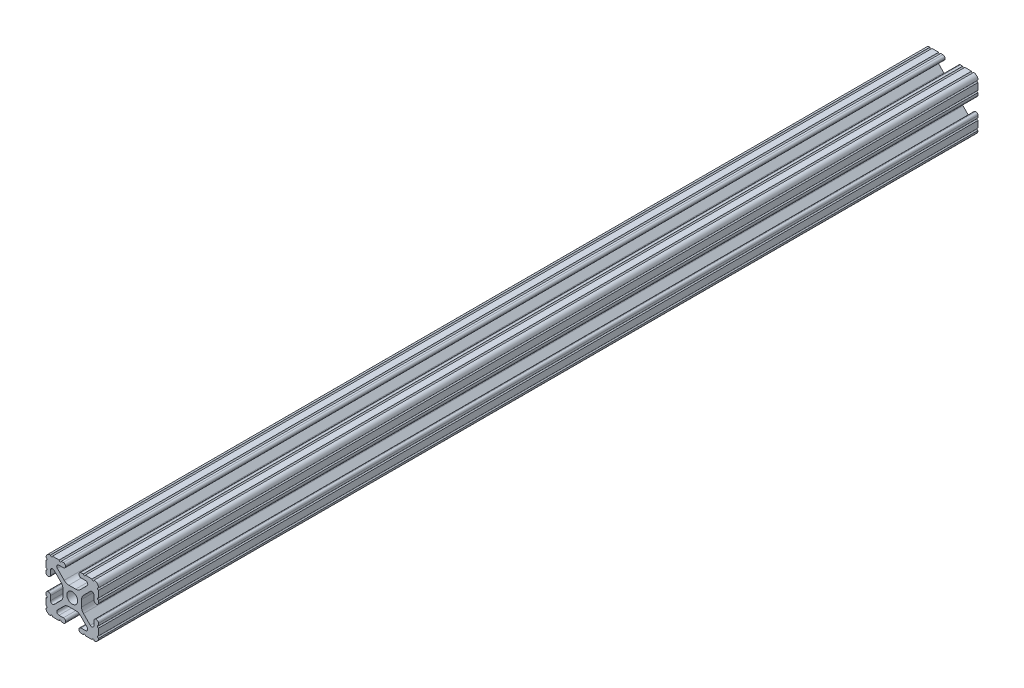
SolidWorks part; units mm, degrees
ref_plane "Front Plane" through (0, 0, 0) normal (0, 0, 1) x (1, 0, 0)
ref_plane "Top Plane" through (0, 0, 0) normal (0, 1, 0) x (1, 0, 0)
ref_plane "Right Plane" through (0, 0, 0) normal (1, 0, 0) x (0, 0, -1)
sketch "Sketch1" plane through (0, 0, 0) normal (0, 0, 1) x (1, 0, 0)
  line L88 (-7.1797, -8.6452) -> (-3.9523, -5.4237)
  line L89 (-1.7093, -4.4958) -> (1.7093, -4.4958)
  line L90 (3.9523, -5.4237) -> (7.1797, -8.6452)
  line L91 (6.4164, -10.4902) -> (4.2875, -10.4902)
  line L92 (3.2385, -11.5392) -> (3.2385, -11.651)
  line L93 (4.2875, -12.7) -> (5.3171, -12.7)
  line L94 (6.3331, -12.7) -> (9.5504, -12.7)
  line L95 (12.7, -9.5504) -> (12.7, -6.3331)
  line L96 (12.7, -5.3171) -> (12.7, -4.2875)
  line L97 (11.651, -3.2385) -> (11.5392, -3.2385)
  line L98 (10.4902, -4.2875) -> (10.4902, -6.4021)
  line L99 (8.7371, -7.1294) -> (5.441, -3.8408)
  line L100 (4.5085, -1.5932) -> (4.5085, 1.5932)
  line L101 (5.441, 3.8408) -> (8.7371, 7.1294)
  line L102 (10.4902, 6.4021) -> (10.4902, 4.2875)
  line L103 (11.5392, 3.2385) -> (11.651, 3.2385)
  line L104 (12.7, 4.2875) -> (12.7, 5.3171)
  line L105 (12.7, 6.3331) -> (12.7, 9.5504)
  line L106 (9.5504, 12.7) -> (6.3331, 12.7)
  line L107 (5.3171, 12.7) -> (4.2875, 12.7)
  line L108 (3.2385, 11.651) -> (3.2385, 11.5392)
  line L109 (4.2875, 10.4902) -> (6.4768, 10.4902)
  line L110 (7.207, 8.7244) -> (3.8983, 5.4232)
  line L111 (1.6558, 4.4958) -> (-1.6558, 4.4958)
  line L112 (-3.8983, 5.4232) -> (-7.207, 8.7244)
  line L113 (-6.4768, 10.4902) -> (-4.2875, 10.4902)
  line L114 (-3.2385, 11.5392) -> (-3.2385, 11.651)
  line L115 (-4.2875, 12.7) -> (-5.3171, 12.7)
  line L116 (-6.3331, 12.7) -> (-9.5504, 12.7)
  line L117 (-12.7, 9.5504) -> (-12.7, 6.3331)
  line L118 (-12.7, 5.3171) -> (-12.7, 4.2875)
  line L119 (-11.651, 3.2385) -> (-11.5392, 3.2385)
  line L120 (-10.4902, 4.2875) -> (-10.4902, 6.4021)
  line L121 (-8.7371, 7.1294) -> (-5.441, 3.8408)
  line L122 (-4.5085, 1.5932) -> (-4.5085, -1.5932)
  line L123 (-5.441, -3.8408) -> (-8.7371, -7.1294)
  line L124 (-10.4902, -6.4021) -> (-10.4902, -4.2875)
  line L125 (-11.5392, -3.2385) -> (-11.651, -3.2385)
  line L126 (-12.7, -4.2875) -> (-12.7, -5.3171)
  line L127 (-12.7, -6.3331) -> (-12.7, -9.5504)
  line L128 (-9.5504, -12.7) -> (-6.3331, -12.7)
  line L129 (-5.3171, -12.7) -> (-4.2875, -12.7)
  line L130 (-3.2385, -11.651) -> (-3.2385, -11.5392)
  line L131 (-4.2875, -10.4902) -> (-6.4164, -10.4902)
  circle A1 centre (0, 0) radius 2.6035
  arc A104 (-7.1797, -8.6452) -> (-6.4164, -10.4902) centre (-6.4164, -9.4098) ccw
  arc A105 (-1.7093, -4.4958) -> (-3.9523, -5.4237) centre (-1.7093, -7.6708) ccw
  arc A106 (3.9523, -5.4237) -> (1.7093, -4.4958) centre (1.7093, -7.6708) ccw
  arc A107 (6.4164, -10.4902) -> (7.1797, -8.6452) centre (6.4164, -9.4098) ccw
  arc A108 (4.2875, -10.4902) -> (3.2385, -11.5392) centre (4.2875, -11.5392) ccw
  arc A109 (3.2385, -11.651) -> (4.2875, -12.7) centre (4.2875, -11.651) ccw
  arc A110 (6.3331, -12.7) -> (5.3171, -12.7) centre (5.8251, -12.7) ccw
  arc A111 (10.5664, -12.6998) -> (9.5504, -12.7) centre (10.0584, -12.7) ccw
  arc A112 (10.5664, -12.6998) -> (12.6998, -10.5664) centre (10.5918, -10.5918) ccw
  arc A113 (12.7, -9.5504) -> (12.6998, -10.5664) centre (12.7, -10.0584) ccw
  arc A114 (12.7, -5.3171) -> (12.7, -6.3331) centre (12.7, -5.8251) ccw
  arc A115 (12.7, -4.2875) -> (11.651, -3.2385) centre (11.651, -4.2875) ccw
  arc A116 (11.5392, -3.2385) -> (10.4902, -4.2875) centre (11.5392, -4.2875) ccw
  arc A117 (8.7371, -7.1294) -> (10.4902, -6.4021) centre (9.4628, -6.4021) ccw
  arc A118 (4.5085, -1.5932) -> (5.441, -3.8408) centre (7.6835, -1.5932) ccw
  arc A119 (5.441, 3.8408) -> (4.5085, 1.5932) centre (7.6835, 1.5932) ccw
  arc A120 (10.4902, 6.4021) -> (8.7371, 7.1294) centre (9.4628, 6.4021) ccw
  arc A121 (10.4902, 4.2875) -> (11.5392, 3.2385) centre (11.5392, 4.2875) ccw
  arc A122 (11.651, 3.2385) -> (12.7, 4.2875) centre (11.651, 4.2875) ccw
  arc A123 (12.7, 6.3331) -> (12.7, 5.3171) centre (12.7, 5.8251) ccw
  arc A124 (12.6998, 10.5664) -> (12.7, 9.5504) centre (12.7, 10.0584) ccw
  arc A125 (12.6998, 10.5664) -> (10.5664, 12.6998) centre (10.5918, 10.5918) ccw
  arc A126 (9.5504, 12.7) -> (10.5664, 12.6998) centre (10.0584, 12.7) ccw
  arc A127 (5.3171, 12.7) -> (6.3331, 12.7) centre (5.8251, 12.7) ccw
  arc A128 (4.2875, 12.7) -> (3.2385, 11.651) centre (4.2875, 11.651) ccw
  arc A129 (3.2385, 11.5392) -> (4.2875, 10.4902) centre (4.2875, 11.5392) ccw
  arc A130 (7.207, 8.7244) -> (6.4768, 10.4902) centre (6.4768, 9.4563) ccw
  arc A131 (1.6558, 4.4958) -> (3.8983, 5.4232) centre (1.6558, 7.6708) ccw
  arc A132 (-3.8983, 5.4232) -> (-1.6558, 4.4958) centre (-1.6558, 7.6708) ccw
  arc A133 (-6.4768, 10.4902) -> (-7.207, 8.7244) centre (-6.4768, 9.4563) ccw
  arc A134 (-4.2875, 10.4902) -> (-3.2385, 11.5392) centre (-4.2875, 11.5392) ccw
  arc A135 (-3.2385, 11.651) -> (-4.2875, 12.7) centre (-4.2875, 11.651) ccw
  arc A136 (-6.3331, 12.7) -> (-5.3171, 12.7) centre (-5.8251, 12.7) ccw
  arc A137 (-10.5664, 12.6998) -> (-9.5504, 12.7) centre (-10.0584, 12.7) ccw
  arc A138 (-10.5664, 12.6998) -> (-12.6998, 10.5664) centre (-10.5918, 10.5918) ccw
  arc A139 (-12.7, 9.5504) -> (-12.6998, 10.5664) centre (-12.7, 10.0584) ccw
  arc A140 (-12.7, 5.3171) -> (-12.7, 6.3331) centre (-12.7, 5.8251) ccw
  arc A141 (-12.7, 4.2875) -> (-11.651, 3.2385) centre (-11.651, 4.2875) ccw
  arc A142 (-11.5392, 3.2385) -> (-10.4902, 4.2875) centre (-11.5392, 4.2875) ccw
  arc A143 (-8.7371, 7.1294) -> (-10.4902, 6.4021) centre (-9.4628, 6.4021) ccw
  arc A144 (-4.5085, 1.5932) -> (-5.441, 3.8408) centre (-7.6835, 1.5932) ccw
  arc A145 (-5.441, -3.8408) -> (-4.5085, -1.5932) centre (-7.6835, -1.5932) ccw
  arc A146 (-10.4902, -6.4021) -> (-8.7371, -7.1294) centre (-9.4628, -6.4021) ccw
  arc A147 (-10.4902, -4.2875) -> (-11.5392, -3.2385) centre (-11.5392, -4.2875) ccw
  arc A148 (-11.651, -3.2385) -> (-12.7, -4.2875) centre (-11.651, -4.2875) ccw
  arc A149 (-12.7, -6.3331) -> (-12.7, -5.3171) centre (-12.7, -5.8251) ccw
  arc A150 (-12.6998, -10.5664) -> (-12.7, -9.5504) centre (-12.7, -10.0584) ccw
  arc A151 (-12.6998, -10.5664) -> (-10.5664, -12.6998) centre (-10.5918, -10.5918) ccw
  arc A152 (-9.5504, -12.7) -> (-10.5664, -12.6998) centre (-10.0584, -12.7) ccw
  arc A153 (-5.3171, -12.7) -> (-6.3331, -12.7) centre (-5.8251, -12.7) ccw
  arc A154 (-4.2875, -12.7) -> (-3.2385, -11.651) centre (-4.2875, -11.651) ccw
  arc A155 (-3.2385, -11.5392) -> (-4.2875, -10.4902) centre (-4.2875, -11.5392) ccw
extrude "Boss-Extrude1" add sketch "Sketch1" along normal mid plane 425.45
